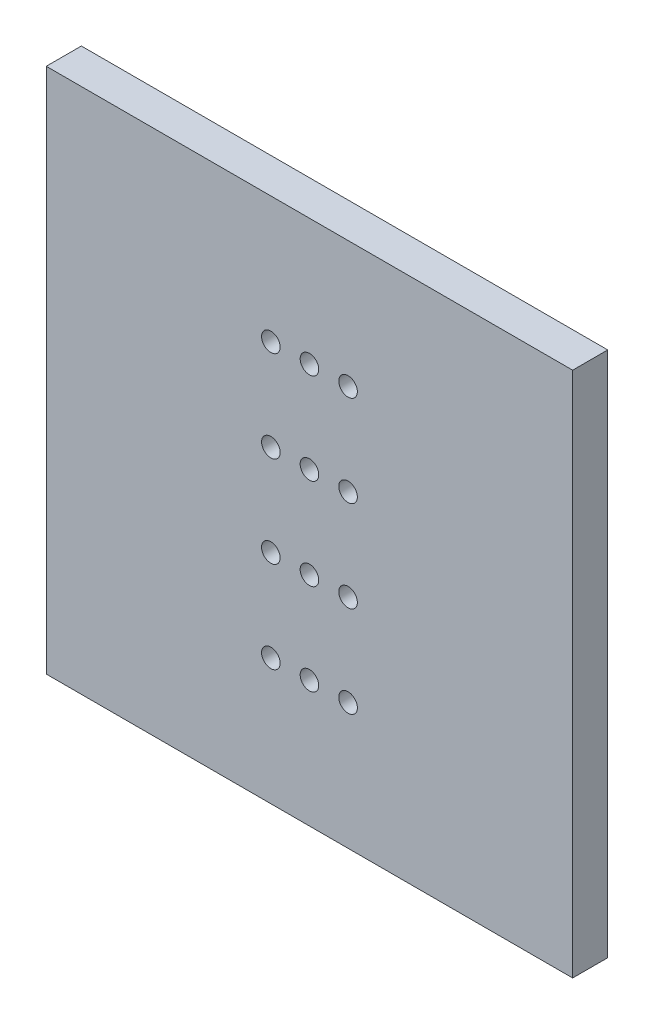
SolidWorks part; units mm, degrees
ref_plane "Plan de face" through (0, 0, 0) normal (0, 0, 1) x (1, 0, 0)
ref_plane "Plan de dessus" through (0, 0, 0) normal (0, 1, 0) x (1, 0, 0)
ref_plane "Plan de droite" through (0, 0, 0) normal (1, 0, 0) x (0, 0, -1)
sketch "Esquisse1" plane through (0, 0, 0) normal (0, 0, 1) x (1, 0, 0)
  line L1 (-15, -15) -> (15, -15)
  line L2 (-15, -15) -> (-15, 15)
  line L3 (-15, 15) -> (15, 15)
  line L4 (15, -15) -> (15, 15)
  line L5 (-15, -15) -> (15, 15) construction
  line L6 (-15, 15) -> (15, -15) construction
  point P0 (0, 0)
extrude "Base_Plate" add sketch "Esquisse1" along normal blind 2
sketch "Sketch_Perforations" plane through (0, 0, 2) normal (0, 0, 1) x (1, 0, 0)
  circle A0 centre (-2.2, -7.8) radius 0.53
  circle A1 centre (-2.2, -2.6) radius 0.53
  circle A2 centre (-2.2, 2.6) radius 0.53
  circle A3 centre (-2.2, 7.8) radius 0.53
  circle A4 centre (0, -7.8) radius 0.53
  circle A5 centre (0, -2.6) radius 0.53
  circle A6 centre (0, 2.6) radius 0.53
  circle A7 centre (0, 7.8) radius 0.53
  circle A8 centre (2.2, -7.8) radius 0.53
  circle A9 centre (2.2, -2.6) radius 0.53
  circle A10 centre (2.2, 2.6) radius 0.53
  circle A11 centre (2.2, 7.8) radius 0.53
extrude "Cut_Perforations" cut sketch "Sketch_Perforations" against normal blind 10
